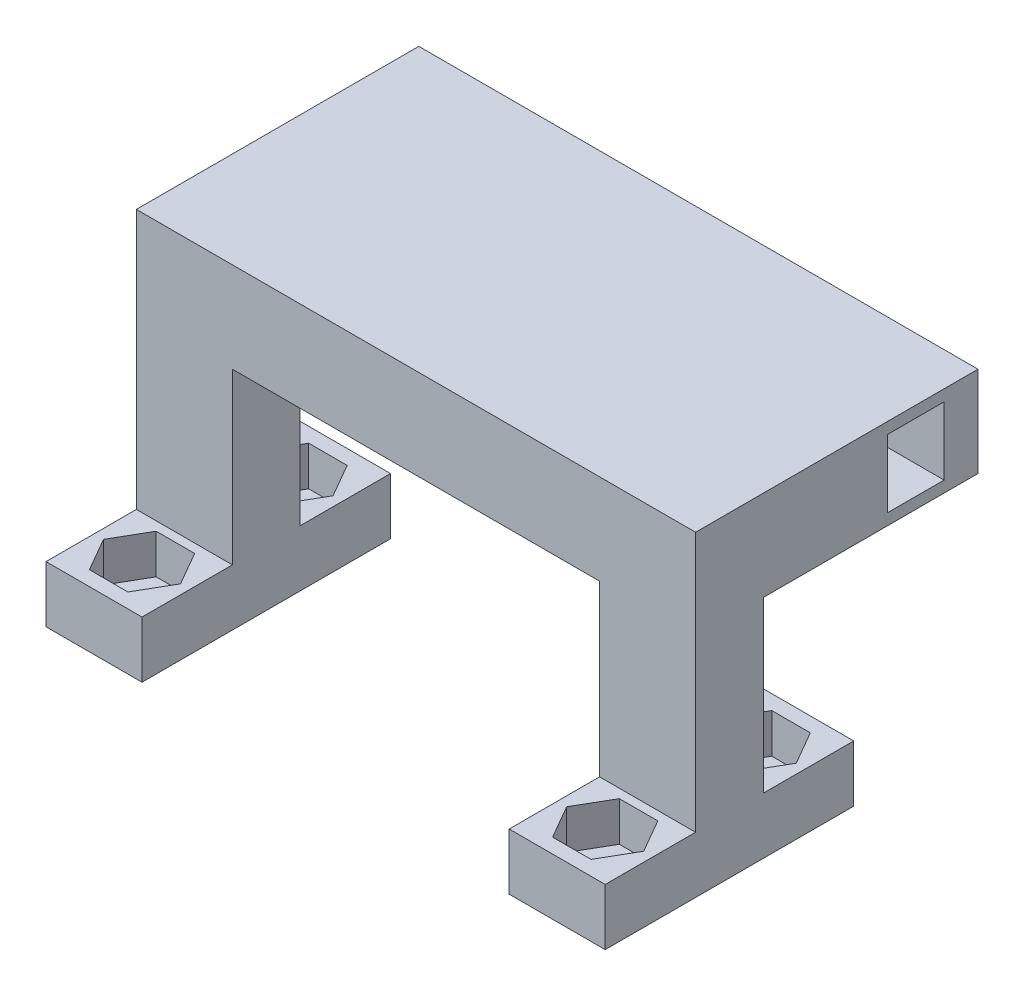
SolidWorks part; units mm, degrees
ref_plane "Front Plane" through (0, 0, 0) normal (0, 0, 1) x (1, 0, 0)
ref_plane "Top Plane" through (0, 0, 0) normal (0, 1, 0) x (1, 0, 0)
ref_plane "Right Plane" through (0, 0, 0) normal (1, 0, 0) x (0, 0, -1)
sketch "Sketch1" plane through (0, 0, 0) normal (0, 1, 0) x (1, 0, 0)
  line L1 (-4.25, -11) -> (4.25, -11)
  line L2 (-4.25, -11) -> (-4.25, 11)
  line L3 (-4.25, 11) -> (4.25, 11)
  line L4 (4.25, -11) -> (4.25, 11)
  line L5 (-4.25, -11) -> (4.25, 11) construction
  line L6 (-4.25, 11) -> (4.25, -11) construction
  point P0 (0, 0)
  dimension "D1" = 22
  dimension "D2" = 8.5
extrude "Boss-Extrude1" add sketch "Sketch1" along normal blind 5
sketch "Sketch2" plane through (0, 5, 0) normal (0, 1, 0) x (1, 0, 0)
  line L0 (-4.25, 2.5) -> (4.25, 2.5) construction
  line L1 (-4.25, 11) -> (-4.25, -11) construction
  line L2 (4.25, -11) -> (4.25, 11) construction
  line L3 (-4.25, -2.5) -> (4.25, -2.5) construction
  line L4 (4.25, 11) -> (-4.25, 11) construction
  line L5 (-4.25, -11) -> (4.25, -11) construction
  line L6 (0, 0) -> (1.3647, 0) construction
  line L7 (-1.705, 9.7031) -> (-3.41, 6.75)
  line L8 (-3.41, 6.75) -> (-1.705, 3.7969)
  line L9 (-1.705, 3.7969) -> (1.705, 3.7969)
  line L10 (1.705, 3.7969) -> (3.41, 6.75)
  line L11 (3.41, 6.75) -> (1.705, 9.7031)
  line L12 (1.705, 9.7031) -> (-1.705, 9.7031)
  line L13 (1.705, -9.7031) -> (-1.705, -9.7031)
  line L14 (3.41, -6.75) -> (1.705, -9.7031)
  line L15 (1.705, -3.7969) -> (3.41, -6.75)
  line L16 (-1.705, -3.7969) -> (1.705, -3.7969)
  line L17 (-3.41, -6.75) -> (-1.705, -3.7969)
  line L18 (-1.705, -9.7031) -> (-3.41, -6.75)
  circle A0 centre (0, 6.75) radius 2.9531 construction
  point P8 (0, 6.75)
  point P12 (0, -6.75)
  dimension "D1" = 2.5
  dimension "D2" = 4.25
  dimension "2.5" = 2.5
  dimension "D3" = 4.25
  dimension "D4" = 3.41
extrude "Cut-Extrude1" cut sketch "Sketch2" against normal blind 3.5
sketch "Sketch3" plane through (0, 1.5, 0) normal (0, 1, 0) x (1, 0, 0)
  line L0 (3.41, 6.75) -> (-3.41, 6.75) construction
  line L1 (3.41, -6.75) -> (-3.41, -6.75) construction
  circle A0 centre (0, 6.75) radius 1.5
  circle A1 centre (0, -6.75) radius 1.5
  circle A2 centre (39, 6.75) radius 1.5
  circle A3 centre (39, -6.75) radius 1.5
  point P16 (0, 0)
  point P17 (0, 0)
  dimension "D1" = 3
  dimension "D2" = 3
  dimension "D3" = 3
  dimension "D5" = 3
  dimension "D4" = 39
extrude "Cut-Extrude2" cut sketch "Sketch3" against normal blind 1.5
sketch "Sketch4" plane through (0, 5, 0) normal (0, 1, 0) x (1, 0, 0)
  line L0 (4.25, -11) -> (4.25, 11) construction
  line L1 (-4.25, -3) -> (4.25, -3)
  line L2 (-4.25, -3) -> (-4.25, 3)
  line L3 (-4.25, 3) -> (4.25, 3)
  line L4 (4.25, -3) -> (4.25, 3)
  line L5 (-4.25, -3) -> (4.25, 3) construction
  line L6 (-4.25, 3) -> (4.25, -3) construction
  point P0 (0, 0)
  dimension "D1" = 6
extrude "Boss-Extrude2" add sketch "Sketch4" along normal blind 23
sketch "Sketch7" plane through (0, 0, 0) normal (0, 1, 0) x (1, 0, 0)
  line L1 (34.75, -11) -> (43.25, -11)
  line L2 (34.75, -11) -> (34.75, 11)
  line L3 (34.75, 11) -> (43.25, 11)
  line L4 (43.25, -11) -> (43.25, 11)
  line L5 (34.75, -11) -> (43.25, 11) construction
  line L6 (34.75, 11) -> (43.25, -11) construction
  point P0 (39, 0)
  point P2 (39, 0)
  point P12 (0, 6.75)
  dimension "D1" = 22
  dimension "D2" = 8.5
extrude "Boss-Extrude4" add sketch "Sketch7" along normal blind 5 separate body
sketch "Sketch8" plane through (0, 5, 0) normal (0, 1, 0) x (1, 0, 0)
  line L0 (43.25, 11) -> (34.75, 11) construction
  line L1 (40.705, 9.7031) -> (37.295, 9.7031)
  line L2 (37.295, 9.7031) -> (35.59, 6.75)
  line L3 (35.59, 6.75) -> (37.295, 3.7969)
  line L4 (37.295, 3.7969) -> (40.705, 3.7969)
  line L5 (40.705, 3.7969) -> (42.41, 6.75)
  line L6 (42.41, 6.75) -> (40.705, 9.7031)
  line L7 (40.705, -3.7969) -> (37.295, -3.7969)
  line L8 (37.295, -3.7969) -> (35.59, -6.75)
  line L9 (35.59, -6.75) -> (37.295, -9.7031)
  line L10 (37.295, -9.7031) -> (40.705, -9.7031)
  line L11 (40.705, -9.7031) -> (42.41, -6.75)
  line L12 (42.41, -6.75) -> (40.705, -3.7969)
  line L13 (34.75, -11) -> (43.25, -11) construction
  circle A0 centre (39, 6.75) radius 2.9531 construction
  circle A1 centre (39, -6.75) radius 2.9531 construction
  point P0 (39, 6.75)
  point P1 (39, -6.75)
  dimension "D1" = 3.41
  dimension "D2" = 3.41
extrude "Cut-Extrude3" cut sketch "Sketch8" against normal blind 3.5
sketch "Sketch9" plane through (0, 1.5, 0) normal (0, 1, 0) x (1, 0, 0)
  circle A0 centre (39, 6.75) radius 1.5
  circle A1 centre (39, -6.75) radius 1.5
extrude "Cut-Extrude4" cut sketch "Sketch9" against normal blind 3.5
sketch "Sketch10" plane through (0, 5, 0) normal (0, 1, 0) x (1, 0, 0)
  line L0 (34.75, 11) -> (34.75, -11) construction
  line L2 (43.25, 3) -> (34.75, 3)
  line L3 (43.25, 3) -> (43.25, -3)
  line L4 (43.25, -3) -> (34.75, -3)
  line L5 (34.75, 3) -> (34.75, -3)
  line L6 (43.25, 3) -> (34.75, -3) construction
  line L7 (43.25, -3) -> (34.75, 3) construction
  point P0 (39, 0)
  point P1 (34.75, -3)
  point P2 (39, 0)
  dimension "D1" = 3
extrude "Boss-Extrude5" add sketch "Sketch10" along normal up to surface (23 mm away) up to face at (0, 28, 0)
sketch "Sketch6" plane through (4.25, 0, 0) normal (1, 0, 0) x (0, 0, -1)
  line L0 (3, 28) -> (3, 5) construction
  line L1 (-3, 28) -> (3, 28)
  line L2 (-3, 28) -> (-3, 20)
  line L3 (-3, 20) -> (3, 20)
  line L4 (3, 28) -> (3, 20)
  dimension "D1" = 8
extrude "Boss-Extrude6" add sketch "Sketch6" along normal up to surface (30.5 mm away) up to face at (34.75, 9.5, 0)
sketch "Sketch11" plane through (0, 0, -3) normal (0, 0, -1) x (-1, 0, 0)
  line L0 (4.25, 28) -> (4.25, 5) construction
  line L1 (-43.25, 28) -> (4.25, 28)
  line L2 (-43.25, 28) -> (-43.25, 20)
  line L3 (-43.25, 20) -> (4.25, 20)
  line L4 (4.25, 28) -> (4.25, 20)
extrude "Boss-Extrude7" add sketch "Sketch11" along normal blind 13.5
sketch "Sketch12" plane through (0, 0, -16.5) normal (0, 0, -1) x (-1, 0, 0)
  line L1 (-43.25, 28) -> (4.25, 28)
  line L2 (-43.25, 28) -> (-43.25, 20)
  line L3 (-43.25, 20) -> (4.25, 20)
  line L4 (4.25, 28) -> (4.25, 20)
extrude "Boss-Extrude8" add sketch "Sketch12" along normal blind 5.5
sketch "Sketch13" plane through (-4.25, 0, 0) normal (-1, 0, 0) x (0, 0, 1)
  line L0 (-22, 20) -> (-22, 28) construction
  line L1 (-19, 21) -> (-14, 21)
  line L2 (-19, 21) -> (-19, 27)
  line L3 (-19, 27) -> (-14, 27)
  line L4 (-14, 21) -> (-14, 27)
  line L5 (-19, 21) -> (-14, 27) construction
  line L6 (-19, 27) -> (-14, 21) construction
  line L7 (-22, 20) -> (-3, 20) construction
  point P0 (-16.5, 24)
  dimension "D1" = 6
  dimension "D2" = 5
  dimension "D3" = 3
  dimension "D4" = 1
extrude "Cut-Extrude5" cut sketch "Sketch13" against normal blind 15
sketch "Sketch14" plane through (0, 0, -22) normal (0, 0, -1) x (-1, 0, 0)
  line L0 (-10.75, 28) -> (-10.75, 20) construction
  line L1 (4.25, 28) -> (-43.25, 28) construction
  line L2 (-43.25, 20) -> (4.25, 20) construction
  line L3 (4.25, 20) -> (4.25, 28) construction
  line L4 (-43.25, 24) -> (4.25, 24) construction
  line L5 (-43.25, 28) -> (-43.25, 20) construction
  line L7 (-10.75, 21) -> (-5.75, 21)
  line L8 (-10.75, 21) -> (-10.75, 27)
  line L9 (-10.75, 27) -> (-5.75, 27)
  line L10 (-5.75, 21) -> (-5.75, 27)
  line L11 (-10.75, 21) -> (-5.75, 27) construction
  line L12 (-10.75, 27) -> (-5.75, 21) construction
  point P12 (-8.25, 24)
  dimension "D1" = 15
  dimension "D2" = 5
  dimension "D3" = 6
  dimension "D4" = 0
extrude "Cut-Extrude6" cut sketch "Sketch14" against normal blind 4
sketch "Sketch15" plane through (43.25, 0, 0) normal (1, 0, 0) x (0, 0, -1)
  line L0 (22, 24) -> (-3, 24) construction
  line L1 (22, 28) -> (22, 20) construction
  line L2 (-3, 28) -> (-3, 5) construction
  line L4 (14, 21) -> (19, 21)
  line L5 (14, 21) -> (14, 27)
  line L6 (14, 27) -> (19, 27)
  line L7 (19, 21) -> (19, 27)
  line L8 (14, 21) -> (19, 27) construction
  line L9 (14, 27) -> (19, 21) construction
  point P6 (16.5, 24)
  dimension "D1" = 6
  dimension "D2" = 5
  dimension "D3" = 3
extrude "Cut-Extrude7" cut sketch "Sketch15" against normal blind 15
sketch "Sketch16" plane through (0, 0, -22) normal (0, 0, -1) x (-1, 0, 0)
  line L0 (-43.25, 24) -> (4.25, 24) construction
  line L1 (-43.25, 28) -> (-43.25, 20) construction
  line L2 (4.25, 20) -> (4.25, 28) construction
  line L3 (-30.25, 20) -> (-30.25, 28) construction
  line L4 (-35.25, 21) -> (-30.25, 21)
  line L5 (-35.25, 21) -> (-35.25, 27)
  line L6 (-35.25, 27) -> (-30.25, 27)
  line L7 (-30.25, 21) -> (-30.25, 27)
  line L8 (-35.25, 21) -> (-30.25, 27) construction
  line L9 (-35.25, 27) -> (-30.25, 21) construction
  line L10 (-43.25, 20) -> (4.25, 20) construction
  line L11 (4.25, 28) -> (-43.25, 28) construction
  point P6 (-32.75, 24)
  dimension "D1" = 13
  dimension "D2" = 0
  dimension "D3" = 5
  dimension "D4" = 6
extrude "Cut-Extrude8" cut sketch "Sketch16" against normal blind 4
sketch "Sketch17" plane through (43.25, 0, 0) normal (1, 0, 0) x (0, 0, -1)
  line L0 (-3, 5) -> (-11, 5)
  line L1 (-11, 5) -> (-11, 0)
  line L2 (-11, 0) -> (11, 0)
  line L3 (11, 0) -> (11, 5)
  line L4 (11, 5) -> (3, 5)
  line L5 (3, 5) -> (3, 20)
  line L6 (3, 20) -> (22, 20)
  line L7 (22, 20) -> (22, 28)
  line L8 (22, 28) -> (-3, 28)
  line L9 (-3, 28) -> (-3, 5)
  line L11 (14, 27) -> (19, 27)
  line L12 (14, 27) -> (14, 21)
  line L13 (14, 21) -> (19, 21)
  line L14 (19, 27) -> (19, 21)
extrude "Boss-Extrude9" add sketch "Sketch17" along normal blind 2
sketch "Sketch18" plane through (0, 5, 0) normal (0, 1, 0) x (1, 0, 0)
  line L1 (34.75, -11) -> (45.25, -11)
  line L2 (34.75, -11) -> (34.75, -3)
  line L3 (34.75, -3) -> (45.25, -3)
  line L4 (45.25, -11) -> (45.25, -3)
  line L5 (34.75, 11) -> (45.25, 11)
  line L6 (34.75, 11) -> (34.75, 3)
  line L7 (34.75, 3) -> (45.25, 3)
  line L8 (45.25, 11) -> (45.25, 3)
extrude "Boss-Extrude10" add sketch "Sketch18" against normal up to surface (5 mm away) up to face at (39, 0, -8.25)
sketch "Sketch20" plane through (34.75, 0, 0) normal (-1, 0, 0) x (0, 0, 1)
  line L0 (-3, 5) -> (-11, 5)
  line L1 (-11, 5) -> (-11, 0)
  line L2 (-11, 0) -> (11, 0)
  line L3 (11, 0) -> (11, 5)
  line L4 (11, 5) -> (3, 5)
  line L5 (3, 5) -> (3, 20)
  line L6 (3, 20) -> (-3, 20)
  line L7 (-3, 20) -> (-3, 5)
extrude "Cut-Extrude9" cut sketch "Sketch20" against normal blind 2
sketch "Sketch23" plane through (0, 5, 0) normal (0, 1, 0) x (1, 0, 0)
  line L0 (45.25, 11) -> (36.75, 11) construction
  line L1 (44.41, -6.75) -> (42.705, -3.7969)
  line L2 (42.705, -3.7969) -> (39.295, -3.7969)
  line L3 (39.295, -3.7969) -> (37.59, -6.75)
  line L4 (37.59, -6.75) -> (39.295, -9.7031)
  line L5 (39.295, -9.7031) -> (42.705, -9.7031)
  line L6 (42.705, -9.7031) -> (44.41, -6.75)
  line L8 (37.59, 6.75) -> (39.295, 3.7969)
  line L9 (39.295, 3.7969) -> (42.705, 3.7969)
  line L10 (42.705, 3.7969) -> (44.41, 6.75)
  line L11 (44.41, 6.75) -> (42.705, 9.7031)
  line L12 (42.705, 9.7031) -> (39.295, 9.7031)
  line L13 (39.295, 9.7031) -> (37.59, 6.75)
  circle A0 centre (41, -6.75) radius 1.5
  circle A1 centre (41, -6.75) radius 2.9531 construction
  circle A2 centre (41, 6.75) radius 1.5
  circle A3 centre (0, 6.75) radius 1.5 construction
  circle A4 centre (41, 6.75) radius 2.9531 construction
  dimension "D1" = 3
  dimension "D4" = 3
  dimension "D6" = 4.25
  dimension "D2" = 41
  dimension "D3" = 3.41
  dimension "D5" = 41
  dimension "D7" = 3.41
extrude "Cut-Extrude10" cut sketch "Sketch23" against normal up to surface (3.5 mm away) contours A2 | A0 | L12 L13 L8 L9 L10 L11 A2 | L5 L6 L1 L2 L3 L4 A0 up to face at (0, 1.5, -5.25)
sketch "Sketch24" plane through (0, 1.5, 0) normal (0, 1, 0) x (1, 0, 0)
  circle A0 centre (41, -6.75) radius 1.5
  circle A1 centre (41, 6.75) radius 1.5
  dimension "D1" = 3
  dimension "D2" = 3
extrude "Cut-Extrude11" cut sketch "Sketch24" against normal up to next
sketch "Sketch25" plane through (28.25, 0, 0) normal (1, 0, 0) x (0, 0, -1)
  line L1 (14, 27) -> (19, 27)
  line L2 (14, 27) -> (14, 21)
  line L3 (14, 21) -> (19, 21)
  line L4 (19, 27) -> (19, 21)
extrude "Boss-Extrude11" add sketch "Sketch25" along normal blind 2
